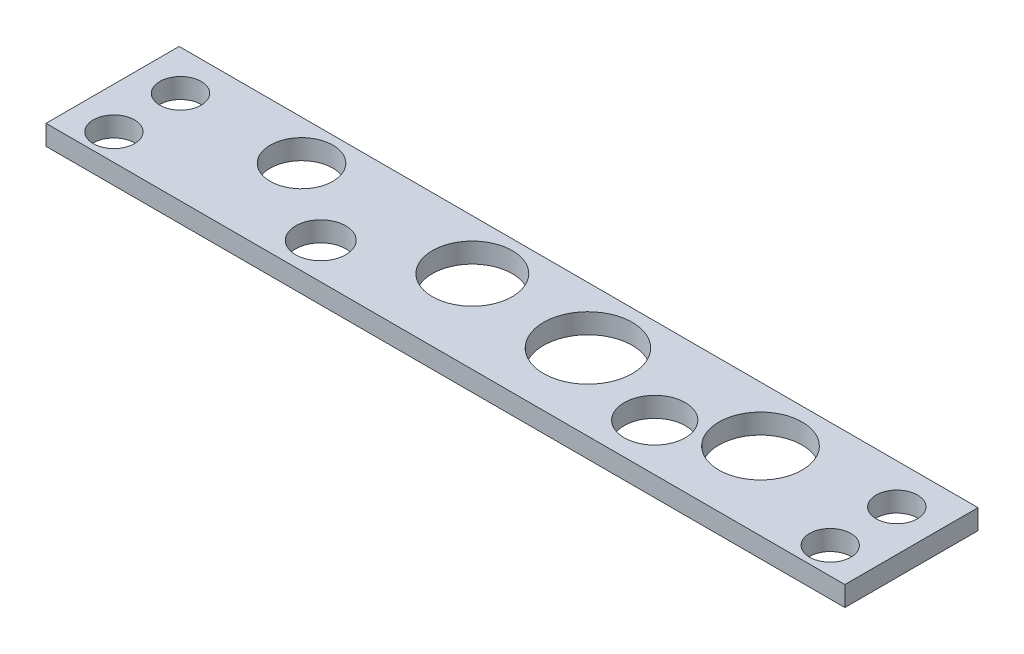
SolidWorks part; units mm, degrees
ref_plane "前视基准面" through (0, 0, 0) normal (0, 0, 1) x (1, 0, 0)
ref_plane "上视基准面" through (0, 0, 0) normal (0, 1, 0) x (1, 0, 0)
ref_plane "右视基准面" through (0, 0, 0) normal (1, 0, 0) x (0, 0, -1)
sketch "草图1" plane through (0, 0, 0) normal (0, 1, 0) x (1, 0, 0)
  line L0 (0, 0) -> (30, 0)
  line L1 (30, 0) -> (30, 10)
  line L2 (30, 10) -> (-30, 10)
  line L3 (-30, 10) -> (-30, 0)
  line L4 (-30, 0) -> (0, 0)
  line L5 (0, 0) -> (26.9, 0)
  line L6 (26.9, 0) -> (26.9, 2) construction
  line L7 (26.9, 2) -> (26.9, 7) construction
  line L8 (0, 0) -> (-26.9, 0)
  line L9 (-26.9, 0) -> (-26.9, 2) construction
  line L10 (-26.9, 2) -> (-26.9, 7) construction
  circle A0 centre (26.9, 2) radius 1.55
  circle A1 centre (26.9, 7) radius 1.55
  circle A2 centre (-26.9, 7) radius 1.55
  circle A3 centre (-26.9, 2) radius 1.55
  circle A4 centre (-17.8084, 7) radius 2.3539
  circle A5 centre (-12.0745, 2.7077) radius 1.884
  circle A6 centre (-4.211, 6.2299) radius 3
  circle A7 centre (4.9632, 5.7384) radius 3.3343
  circle A8 centre (12.1714, 3.55) radius 2.2902
  circle A9 centre (17.8234, 5.8402) radius 3.1274
extrude "凸台-拉伸1" add sketch "草图1" along normal blind 1.5 contours L3 L4 L0 L1 L2 A9 A8 A7 A6 A5 A4 A3 A2 A1 A0
